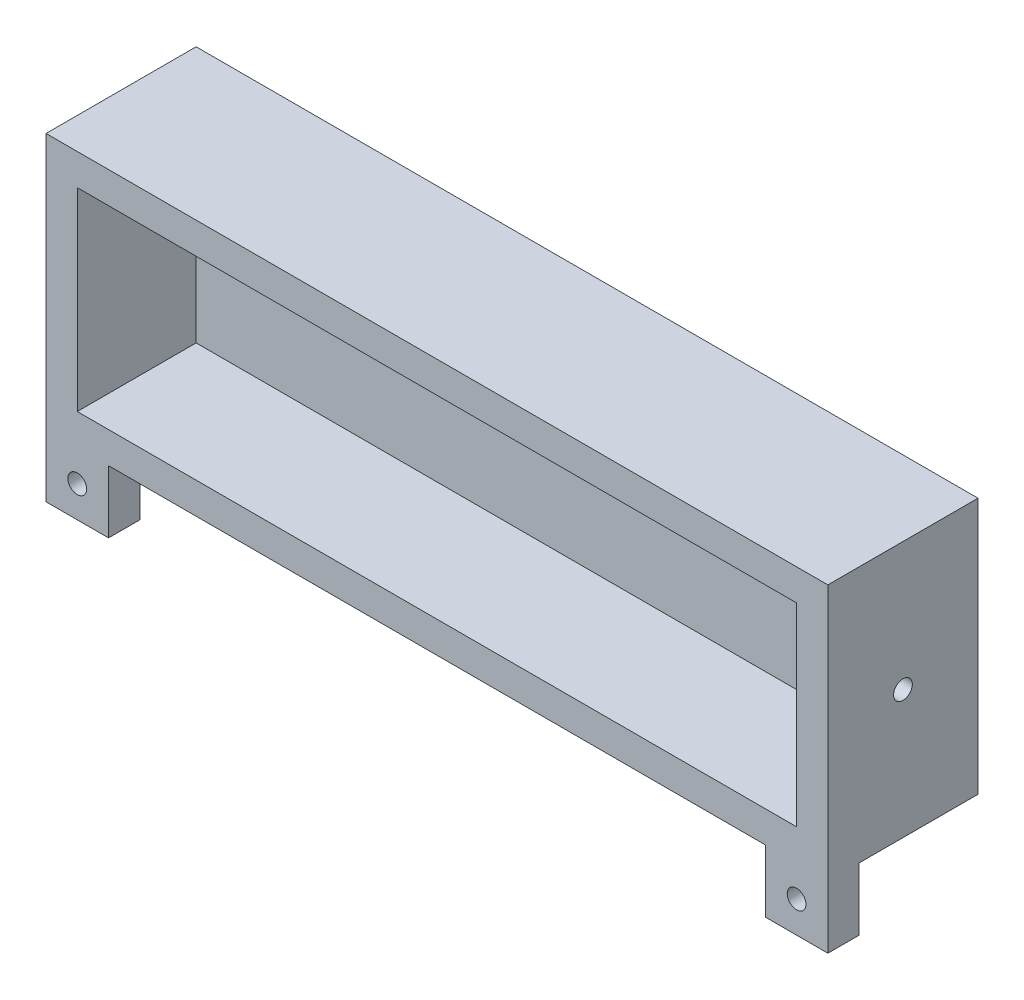
SolidWorks part; units mm, degrees
material "ABS"
ref_plane "Front Plane" through (0, 0, 0) normal (0, 0, 1) x (1, 0, 0)
ref_plane "Top Plane" through (0, 0, 0) normal (0, 1, 0) x (1, 0, 0)
ref_plane "Right Plane" through (0, 0, 0) normal (1, 0, 0) x (0, 0, -1)
sketch "Sketch1" plane through (0, 0, 0) normal (0, 0, 1) x (1, 0, 0)
  line L1 (0, 0) -> (115, 0)
  line L2 (0, 0) -> (0, 31)
  line L3 (0, 31) -> (115, 31)
  line L4 (115, 0) -> (115, 31)
  dimension "D1" = 31
  dimension "D2" = 115
extrude "Boss-Extrude1" add sketch "Sketch1" along normal blind 19
shell "Shell1" thickness 5
sketch "Sketch2" plane through (120, 0, 0) normal (1, 0, 0) x (0, 0, -1)
  line L0 (-19, -5) -> (5, -5) construction
  line L1 (-19, -5) -> (-19, 36) construction
  circle A0 centre (-7, 15.5) radius 1.5
  point P4 (-7, -5)
  point P7 (-19, 15.5)
  dimension "D1" = 3
extrude "Cut-Extrude1" cut sketch "Sketch2" against normal blind 19
sketch "Sketch3" plane through (0, -5, 0) normal (0, -1, 0) x (-1, 0, 0)
  line L1 (5, -19) -> (-5, -19)
  line L2 (5, -19) -> (5, -14)
  line L3 (5, -14) -> (-5, -14)
  line L4 (-5, -19) -> (-5, -14)
  line L5 (-120, -19) -> (-110, -19)
  line L6 (-120, -19) -> (-120, -14)
  line L7 (-120, -14) -> (-110, -14)
  line L8 (-110, -19) -> (-110, -14)
  dimension "D1" = 10
  dimension "D2" = 5
extrude "Boss-Extrude2" add sketch "Sketch3" along normal blind 10
sketch "Sketch4" plane through (0, 0, 14) normal (0, 0, -1) x (-1, 0, 0)
  line L0 (-110, -15) -> (-120, -15) construction
  line L1 (-120, -15) -> (-120, -5) construction
  line L2 (-5, -15) -> (-5, -5) construction
  line L3 (5, -15) -> (-5, -15) construction
  circle A0 centre (0, -10) radius 1.5
  circle A1 centre (-115, -10) radius 1.5
  point P6 (-115, -15)
  point P9 (-120, -10)
  point P12 (-5, -10)
  point P16 (0, -15)
  dimension "D1" = 3
  dimension "D2" = 3
extrude "Cut-Extrude2" cut sketch "Sketch4" against normal through all
ref_plane "Plane1" through (0, 15.5, 0) normal (0, 1, 0) x (1, 0, 0)
